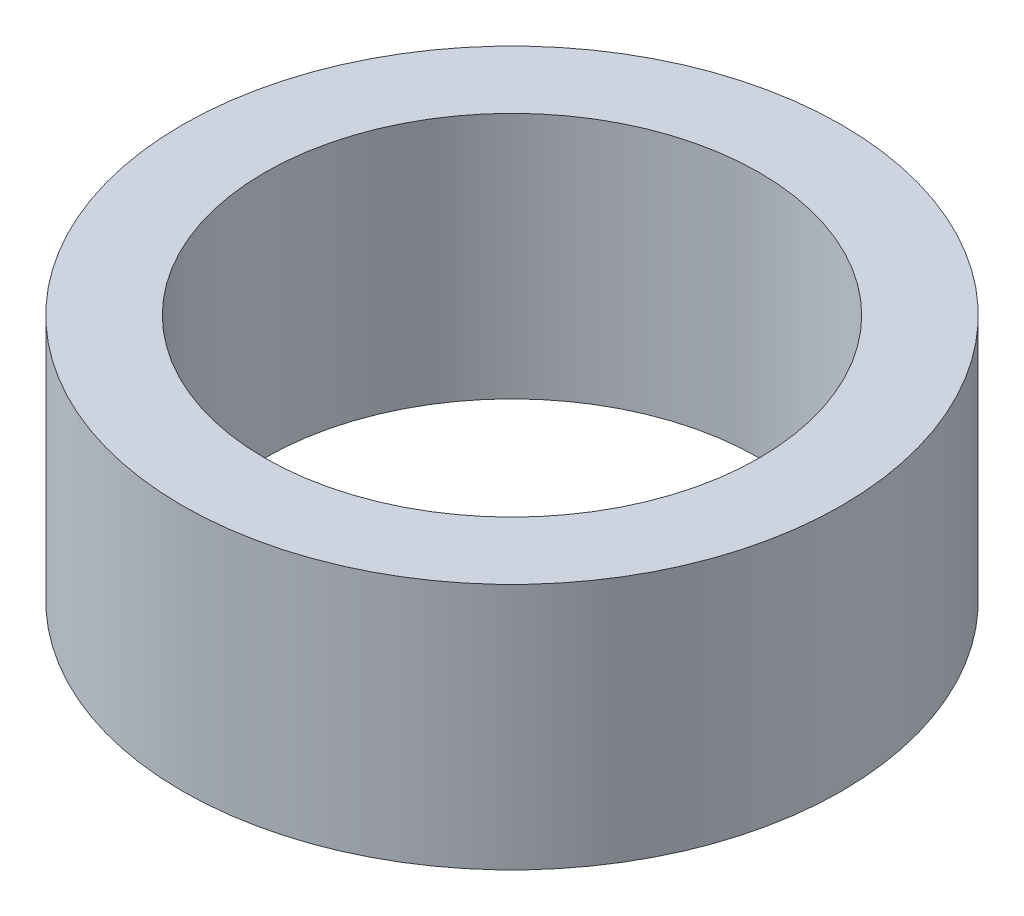
SolidWorks part; units mm, degrees
material "ABS PC"
ref_plane "Plan de face" through (0, 0, 0) normal (0, 0, 1) x (1, 0, 0)
ref_plane "Plan de dessus" through (0, 0, 0) normal (0, 1, 0) x (1, 0, 0)
ref_plane "Plan de droite" through (0, 0, 0) normal (1, 0, 0) x (0, 0, -1)
sketch "Esquisse2" plane through (0, 0, 0) normal (0, 1, 0) x (1, 0, 0)
  circle A0 centre (0, 0) radius 8
  circle A1 centre (0, 0) radius 6
  dimension "D1" = 12
  dimension "D2" = 16
extrude "Boss.-Extru.1" add sketch "Esquisse2" along normal blind 6
